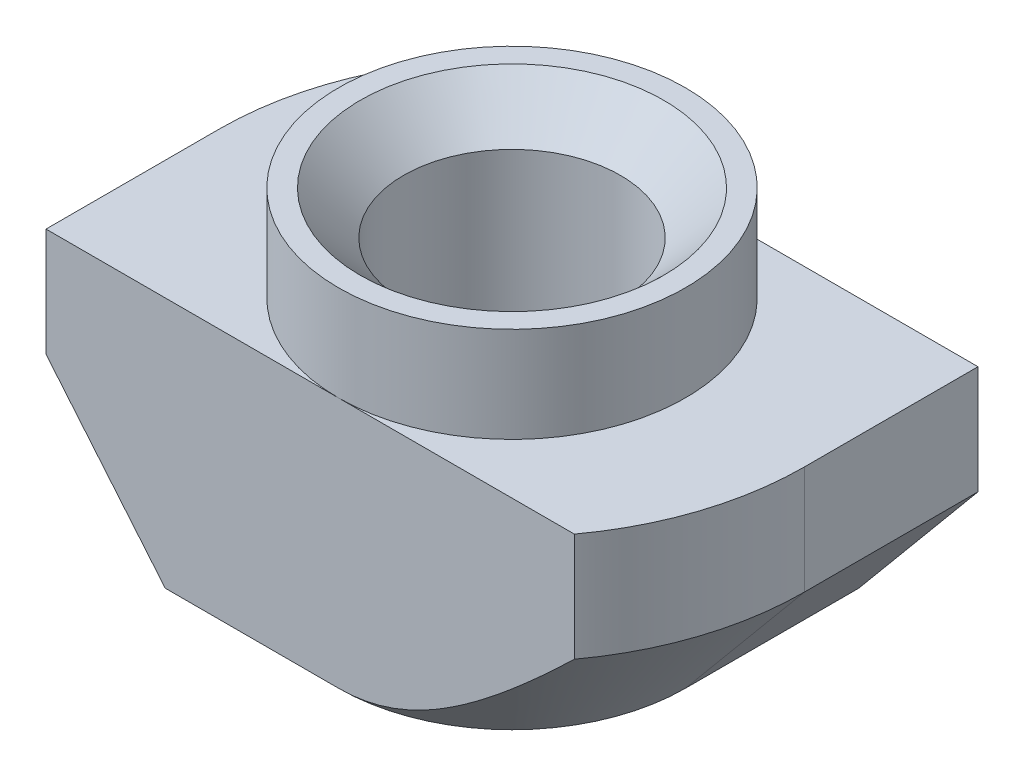
SolidWorks part; units mm, degrees
material "Сталь 20  ГОСТ 1050-2013"
ref_plane "Спереди" through (0, 0, 0) normal (0, 0, 1) x (1, 0, 0)
ref_plane "Сверху" through (0, 0, 0) normal (0, 1, 0) x (1, 0, 0)
ref_plane "Справа" through (0, 0, 0) normal (1, 0, 0) x (0, 0, -1)
sketch "Эскиз1" plane through (0, 0, 0) normal (0, 0, 1) x (1, 0, 0)
  line L0 (4, 0) -> (-4, 0)
  line L1 (-4, 0) -> (-4, -2.2)
  line L2 (-4, -2.2) -> (-6.75, -2.2)
  line L3 (-6.75, -2.2) -> (-6.75, -8)
  line L4 (-6.75, -8) -> (6.75, -8)
  line L5 (0, -8) -> (0, 0) construction
  line L6 (6.75, -2.2) -> (6.75, -8)
  line L7 (4, -2.2) -> (6.75, -2.2)
  line L8 (4, 0) -> (4, -2.2)
  dimension "D1" = 8
  dimension "D2" = 13.5
  dimension "D3" = 8
  dimension "D4" = 2.2
extrude "Бобышка-Вытянуть1" add sketch "Эскиз1" along normal mid plane 8
hole_wizard "Отверстие обработанное метчиком M62" positions "Эскиз2" profile "Эскиз3" tap size "M6" standard "ISO" end condition up to next
sketch "Эскиз2" plane through (0, 0, 0) normal (0, 1, 0) x (1, 0, 0)
  point P0 (0, 0)
sketch "Эскиз3" plane through (0, 0, 0) normal (1, 0, 0) x (0, 0, 1)
  line L0 (0, 0) -> (0, 8)
  line L1 (0, 8) -> (3.5, 8)
  line L2 (2.5, 7) -> (2.5, 1)
  line L3 (2.5, 1) -> (3.5, 0)
  line L5 (3.5, 0) -> (0, 0)
  line L6 (-2.5, 1) -> (-3.5, 0) construction
  line L7 (3.5, 8) -> (2.5, 7)
  line L8 (-3.5, 8) -> (-2.5, 7) construction
  line L11 (0, -6.35) -> (0, 107.95) construction
  dimension "Диаметр проходного сверла" = 5
  dimension "Глубина проходного сверла" = 8
  dimension "Диаметр передней зенковки" = 7
  dimension "Угол передней зенковки" = 90
  dimension "Диаметр задней зенковки" = 7
  dimension "Угол задней зенковки" = 90
cosmetic thread "Отверстие резьбы2" parameters "D2"=6
sketch "Эскиз4" plane through (0, 0, 0) normal (0, 1, 0) x (1, 0, 0)
  line L8 (-4, -4) -> (-4, 4) construction
  circle A2 centre (0, 0) radius 4
extrude "Вырез-Вытянуть1" cut sketch "Эскиз4" against normal up to surface (2.2 mm away) flip side to cut up to face at (-5.375, -2.2, 0)
sketch "Эскиз5" plane through (0, -2.2, 0) normal (0, 1, 0) x (1, 0, 0)
  line L0 (-6.75, 0) -> (-6.75, 4)
  line L1 (-6.75, -4) -> (-6.75, 4) construction
  line L2 (-6.75, 4) -> (-5.4371, 4)
  line L3 (0, 4) -> (-6.75, 4) construction
  line L4 (6.75, 0) -> (6.75, -4)
  line L5 (6.75, -4) -> (6.75, 4) construction
  line L6 (6.75, -4) -> (5.4371, -4)
  line L7 (6.75, -4) -> (0, -4) construction
  arc A0 (-5.4371, 4) -> (-6.75, 0) centre (0, 0) ccw
  arc A2 (6.75, 0) -> (5.4371, -4) centre (0, 0) cw
extrude "Вырез-Вытянуть2" cut sketch "Эскиз5" against normal through all
sketch "Эскиз6" plane through (0, 0, 4) normal (0, 0, 1) x (1, 0, 0)
  line L0 (-6.75, -4.7) -> (-6.75, -8)
  line L1 (-6.75, -2.2) -> (-6.75, -8) construction
  line L2 (-6.75, -8) -> (-4, -8)
  line L3 (-6.75, -8) -> (5.4371, -8) construction
  line L4 (-4, -8) -> (-6.75, -4.7)
  line L5 (0, -2.2) -> (-6.75, -2.2) construction
  line L7 (-4, 0) -> (-4, -2.2) construction
  point P10 (0, 0)
  dimension "D1" = 2.5
sketch "Эскиз7" plane through (0, -8, 0) normal (0, -1, 0) x (1, 0, 0)
  line L0 (0, 6.75) -> (-6.75, 6.75)
  line L1 (-6.75, 6.75) -> (-6.75, 0)
  line L2 (0, -6.75) -> (6.75, -6.75)
  line L3 (6.75, -6.75) -> (6.75, 0)
  arc A0 (-6.75, 0) -> (0, -6.75) centre (0, 0) ccw
  arc A1 (6.75, 0) -> (0, 6.75) centre (0, 0) ccw
sweep "Вырез-По траектории1" cut profiles "Эскиз6" path "Эскиз7"
